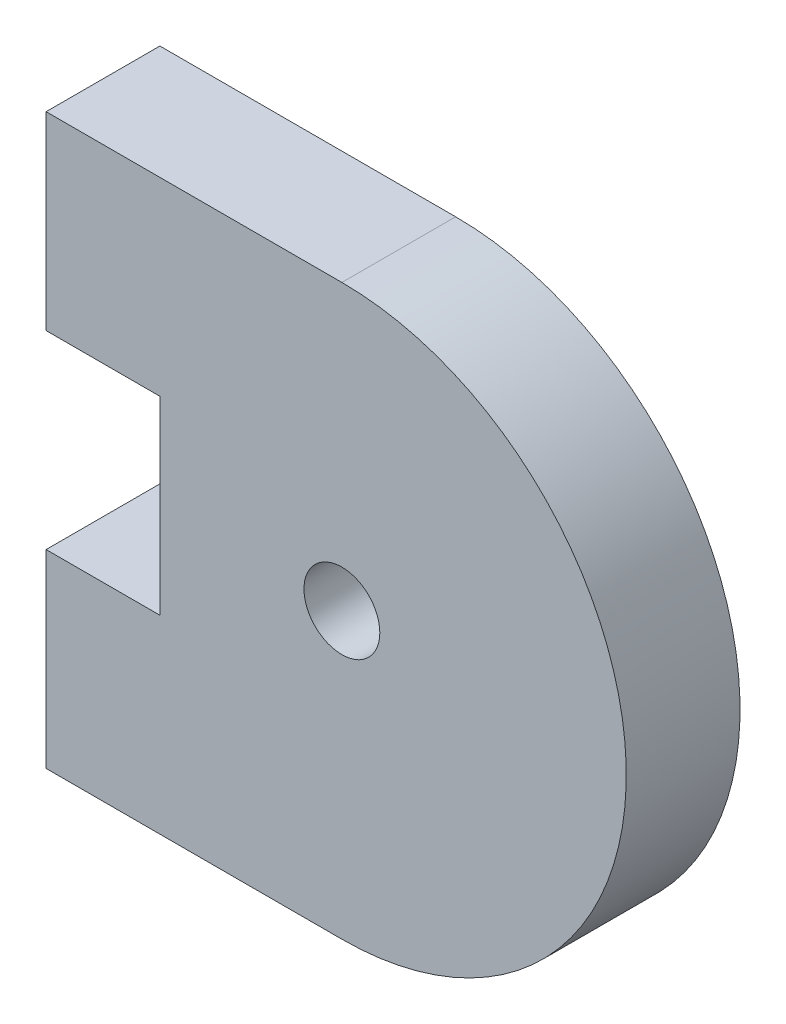
SolidWorks part; units mm, degrees
ref_plane "Alzado" through (0, 0, 0) normal (0, 0, 1) x (1, 0, 0)
ref_plane "Planta" through (0, 0, 0) normal (0, 1, 0) x (1, 0, 0)
ref_plane "Vista lateral" through (0, 0, 0) normal (1, 0, 0) x (0, 0, -1)
sketch "Corte exterior" plane through (0, 0, 0) normal (0, 0, 1) x (1, 0, 0)
  line L0 (42.4, 49.8786) -> (34.6, 49.8786)
  line L1 (34.6, 49.8786) -> (34.6, 44.8786)
  line L2 (34.6, 44.8786) -> (37.6, 44.8786)
  line L3 (37.6, 44.8786) -> (37.6, 39.8786)
  line L4 (37.6, 39.8786) -> (34.6, 39.8786)
  line L5 (34.6, 39.8786) -> (34.6, 34.8786)
  line L6 (34.6, 34.8786) -> (42.4, 34.8786)
  circle A0 centre (42.4, 42.3786) radius 1
  arc A1 (42.4, 34.8786) -> (42.4, 49.8786) centre (42.4, 42.3786) ccw
  dimension "D1" = 4.8
  dimension "D2" = 3
  dimension "D3" = 3
extrude "Saliente-Extruir1" add sketch "Corte exterior" along normal blind 3
